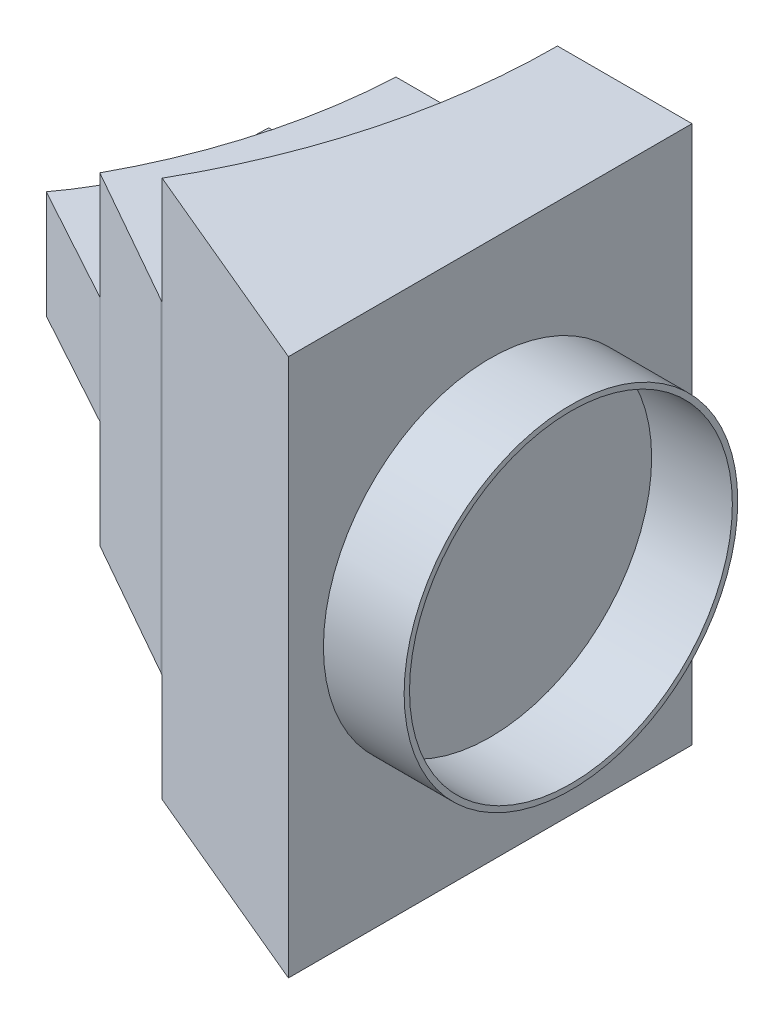
SolidWorks part; units mm, degrees
ref_plane "Front Plane" through (0, 0, 0) normal (0, 0, 1) x (1, 0, 0)
ref_plane "Top Plane" through (0, 0, 0) normal (0, 1, 0) x (1, 0, 0)
ref_plane "Right Plane" through (0, 0, 0) normal (1, 0, 0) x (0, 0, -1)
sketch "Sketch3" plane through (0, 0, 0) normal (0, 1, 0) x (1, 0, 0)
  line L1 (0, 0) -> (0, 11.265) construction
  line L7 (87.761, -47.9376) -> (113.878, -62.6991)
  line L8 (99.8749, -5) -> (129.8749, -5)
  line L9 (113.878, -62.6991) -> (114.4068, -63.0027)
  arc A0 (95.9613, -28.1322) -> (87.761, -47.9376) centre (0, 0) cw
  arc A1 (99.8749, -5) -> (95.9613, -28.1322) centre (0, 0) cw
  arc A2 (129.8749, -5) -> (114.4068, -63.0027) centre (13.3909, -5) cw
  dimension "D4" = 30
extrude "Boss-Extrude1" add sketch "Sketch3" along normal blind 60
ref_plane "Plane1" through (0, 30, 0) normal (0, 1, 0) x (1, 0, 0)
sketch "Sketch4" plane through (0, 30, 0) normal (0, 1, 0) x (1, 0, 0)
  line L0 (87.761, -47.9376) -> (65.8207, -35.9532)
  line L2 (99.8749, -5) -> (76.2039, -5)
  arc A0 (99.8749, -5) -> (87.761, -47.9376) centre (0, 0) cw
  arc A2 (65.8207, -35.9532) -> (76.2039, -5) centre (24.8749, -5) ccw
  dimension "D1" = 25
  dimension "D2" = 75
extrude "Boss-Extrude2" add sketch "Sketch4" along normal mid plane 20
sketch "Sketch5" plane through (0, 30, 0) normal (0, 1, 0) x (1, 0, 0)
  line L1 (129.8749, -5) -> (154.8749, -5)
  line L4 (154.8749, -5) -> (154.8749, -63.0027)
  line L5 (114.4068, -63.0027) -> (154.8749, -80)
  line L6 (154.8749, -80) -> (154.8749, -63.0027)
  arc A0 (129.8749, -5) -> (114.4068, -63.0027) centre (13.3909, -5) cw
  dimension "D1" = 25
  dimension "D2" = 75
extrude "Boss-Extrude3" add sketch "Sketch5" along normal mid plane 100
sketch "Sketch6" plane through (154.8749, 0, 0) normal (1, 0, 0) x (0, 0, -1)
  line L0 (41.25, 30) -> (-41.25, 30) construction
  circle A0 centre (-42.5, 30) radius 31
  circle A1 centre (-42.5, 30) radius 30
  dimension "D1" = 60
  dimension "D2" = 62
extrude "Boss-Extrude4" add sketch "Sketch6" along normal blind 15
